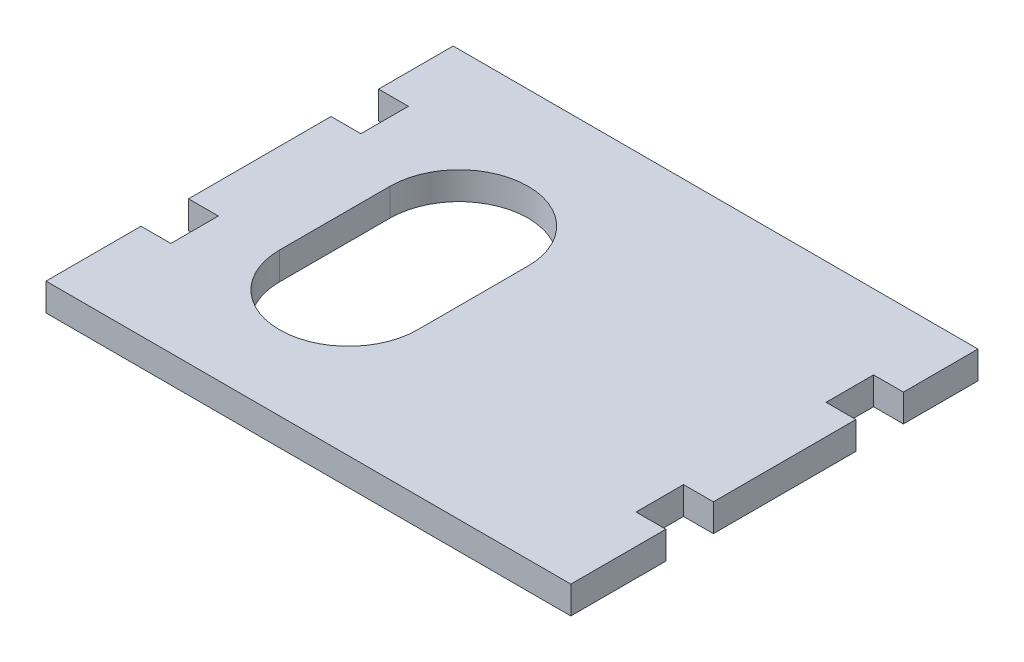
SolidWorks part; units mm, degrees
ref_plane "Front Plane" through (0, 0, 0) normal (0, 0, 1) x (1, 0, 0)
ref_plane "Top Plane" through (0, 0, 0) normal (0, 1, 0) x (1, 0, 0)
ref_plane "Right Plane" through (0, 0, 0) normal (1, 0, 0) x (0, 0, -1)
sketch "Sketch1" plane through (0, 0, 0) normal (0, 1, 0) x (1, 0, 0)
  line L1 (-44.4495, 24.5126) -> (50.5505, 24.5126)
  line L2 (-44.4495, 24.5126) -> (-44.4495, -49.1874)
  line L3 (-44.4495, -49.1874) -> (50.5505, -49.1874)
  line L4 (50.5505, 24.5126) -> (50.5505, -49.1874)
  dimension "D1" = 95
  dimension "D2" = 73.7
extrude "Boss-Extrude1" add sketch "Sketch1" along normal blind 5 contours L1 L4 L3 L2
sketch "Sketch2" plane through (0, 5, 0) normal (0, 1, 0) x (1, 0, 0)
  line L0 (-44.4495, 24.5126) -> (50.5505, 24.5126) construction
  line L1 (-44.4495, 11.0126) -> (-39.0495, 11.0126)
  line L2 (-44.4495, 11.0126) -> (-44.4495, 2.4126)
  line L3 (-44.4495, 2.4126) -> (-39.0495, 2.4126)
  line L4 (-39.0495, 11.0126) -> (-39.0495, 2.4126)
  line L5 (-44.4495, -23.3874) -> (-39.0495, -23.3874)
  line L6 (-44.4495, -23.3874) -> (-44.4495, -31.9874)
  line L7 (-44.4495, -31.9874) -> (-39.0495, -31.9874)
  line L8 (-39.0495, -23.3874) -> (-39.0495, -31.9874)
  line L9 (45.1505, 11.0126) -> (50.5505, 11.0126)
  line L10 (45.1505, 11.0126) -> (45.1505, 2.4126)
  line L11 (45.1505, 2.4126) -> (50.5505, 2.4126)
  line L12 (50.5505, 11.0126) -> (50.5505, 2.4126)
  line L13 (45.1505, -23.3874) -> (50.5505, -23.3874)
  line L14 (45.1505, -23.3874) -> (45.1505, -31.9874)
  line L15 (45.1505, -31.9874) -> (50.5505, -31.9874)
  line L16 (50.5505, -23.3874) -> (50.5505, -31.9874)
  line L17 (-44.4495, -49.1874) -> (50.5505, -49.1874) construction
  line L18 (-44.4495, 24.5126) -> (-44.4495, -49.1874) construction
  line L19 (50.5505, 24.5126) -> (50.5505, -49.1874) construction
  dimension "D1" = 5.4
  dimension "D2" = 8.6
  dimension "D3" = 13.5
  dimension "D4" = 17.2
extrude "Cut-Extrude1" cut sketch "Sketch2" against normal up to next
sketch "Sketch3" plane through (0, 5, 0) normal (0, 1, 0) x (1, 0, 0)
  line L0 (-15.6856, -3.1885) -> (-15.6856, -23.1885) construction
  line L1 (-3.1856, -3.1885) -> (-3.1856, -23.1885)
  line L2 (-28.1856, -3.1885) -> (-28.1856, -23.1885)
  arc A0 (-3.1856, -3.1885) -> (-28.1856, -3.1885) centre (-15.6856, -3.1885) ccw
  arc A1 (-28.1856, -23.1885) -> (-3.1856, -23.1885) centre (-15.6856, -23.1885) ccw
  point P2 (-15.6856, -13.1885)
  dimension "D1" = 25
  dimension "D2" = 20
extrude "Cut-Extrude2" cut sketch "Sketch3" against normal up to next
